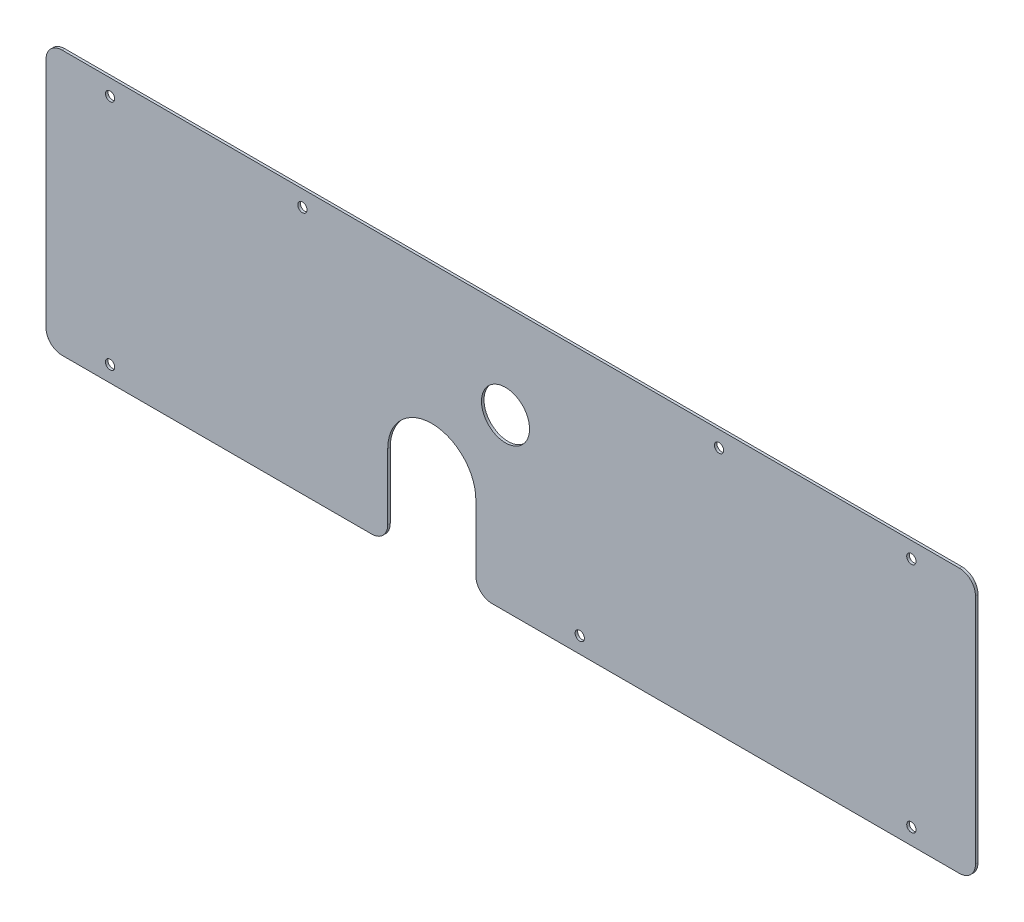
SolidWorks part; units mm, degrees
material "1060 Alloy"
ref_plane "Front Plane" through (0, 0, 0) normal (0, 0, 1) x (1, 0, 0)
ref_plane "Top Plane" through (0, 0, 0) normal (0, 1, 0) x (1, 0, 0)
ref_plane "Right Plane" through (0, 0, 0) normal (1, 0, 0) x (0, 0, -1)
sketch "Sketch1" plane through (0, 0, 0) normal (0, 0, 1) x (1, 0, 0)
  line L0 (-31.7213, -10.77) -> (-31.7213, -61.8098)
  line L1 (-244.9575, 103.1698) -> (335.0425, 103.1698)
  line L2 (-244.9575, 103.1698) -> (-244.9575, -61.8098)
  line L3 (-244.9575, -61.8098) -> (-31.7213, -61.8098)
  line L4 (335.0425, 103.1698) -> (335.0425, -61.8098)
  line L5 (23.2787, -10.77) -> (23.2787, -61.8098)
  line L6 (23.2787, -61.8098) -> (335.0425, -61.8098)
  line L8 (-244.9575, -43.8266) -> (-244.9575, -48.5256) construction
  line L9 (335.0425, -43.8266) -> (335.0425, -48.5256) construction
  line L10 (333.0359, 103.1698) -> (335.0425, 103.1698) construction
  line L11 (335.0425, -61.8098) -> (335.0425, -59.8032) construction
  line L12 (335.0425, -61.8098) -> (-244.9575, -61.8098) construction
  line L13 (11.7787, 55.18) -> (11.7787, 29.0057) construction
  arc A0 (23.2787, -10.77) -> (-31.7213, -10.77) centre (-4.2213, -10.77) ccw
  circle A1 centre (41.7787, 44.23) radius 15
  circle A2 centre (-4.2213, -10.77) radius 19.05 construction
  dimension "D1" = 55
  dimension "D3" = 30
  dimension "D4" = 55
  dimension "D5" = 30
  dimension "D2" = 0
extrude "Boss-Extrude1" add sketch "Sketch1" along normal blind 1.5875
sketch "Sketch3" plane through (0, 0, 1.5875) normal (0, 0, 1) x (1, 0, 0)
  line L0 (335.0425, 103.1698) -> (-244.9575, 103.1698) construction
  line L1 (-244.9575, 103.1698) -> (-244.9575, -61.8098) construction
  line L2 (-244.9575, -61.8098) -> (-31.7213, -61.8098) construction
  line L4 (335.0425, -61.8098) -> (335.0425, 103.1698) construction
  point P0 (-204.9575, 93.1698)
  point P1 (295.0425, 93.1698)
  point P2 (295.0425, -51.8098)
  point P3 (-204.9575, -51.8098)
  point P4 (88.1218, 93.1698)
  point P5 (88.1218, -51.8098)
  dimension "D1" = 10
  dimension "D2" = 293.0793
  dimension "D4" = 40
  dimension "D5" = 10
  dimension "D3" = 40
hole_wizard "M5 Clearance Hole1" positions "Sketch4" profile "Sketch5" hole size "M5" standard "ANSI Metric" end condition through all
sketch "Sketch4" plane through (0, 0, 1.5875) normal (0, 0, 1) x (1, 0, 0)
  line L0 (335.0425, -61.8098) -> (335.0425, 103.1698) construction
  point P0 (-204.9575, 93.1698)
  point P3 (-204.9575, -51.8098)
  point P9 (88.1218, -51.8098)
  point P12 (295.0425, -51.8098)
  point P20 (-84.9575, 93.1698)
  point P22 (175.0425, 93.1698)
  point P23 (295.0425, 93.1698)
  dimension "D1" = 120
  dimension "D2" = 120
  dimension "D3" = 40
sketch "Sketch5" plane through (-204.9575, 93.1698, 1.5875) normal (1, 0, 0) x (0, -1, 0)
  line L0 (0, 0) -> (0, 1.5875)
  line L1 (0, 1.5875) -> (2.9, 1.5875)
  line L2 (2.9, 1.5875) -> (2.9, 0)
  line L5 (2.9, 0) -> (0, 0)
  line L11 (0, -6.35) -> (0, 107.95) construction
  dimension "Thru Hole Dia." = 5.8
  dimension "Thru Hole Depth" = 1.5875
fillet "Fillet1" radius 10 6 edges at (23.2787, -61.8098, 0.7937) (-31.7213, -61.8098, 0.7937) (-244.9575, 103.1698, 0.7937) (-244.9575, -61.8098, 0.7937) (335.0425, 103.1698, 0.7937) (335.0425, -61.8098, 0.7937)
equation "\"D4@Sketch3\"=\"D3@Sketch3\""
